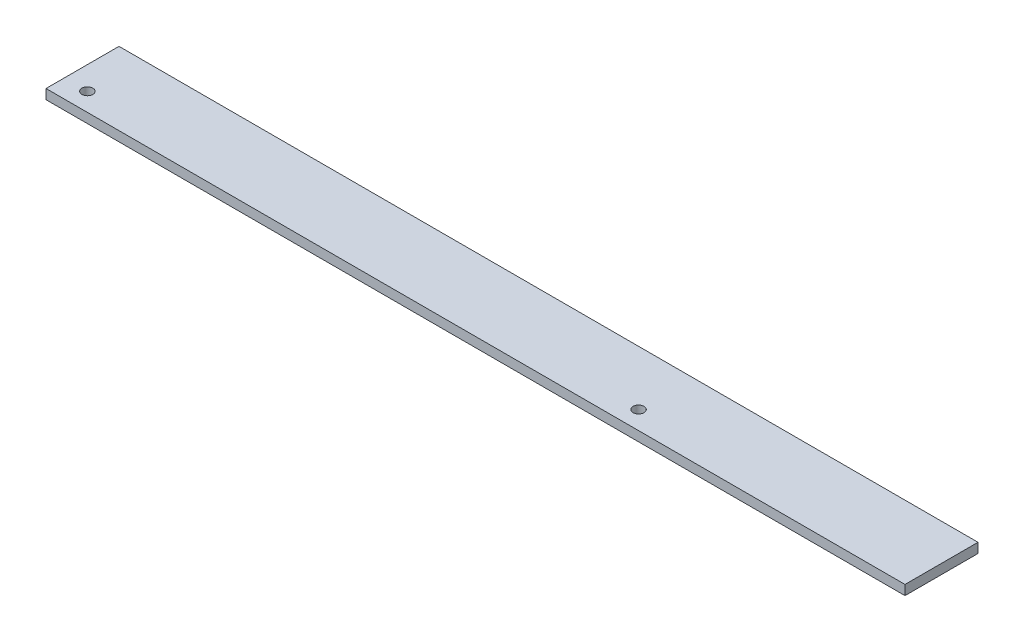
SolidWorks part; units mm, degrees
ref_plane "Спереди" through (0, 0, 0) normal (0, 0, 1) x (1, 0, 0)
ref_plane "Сверху" through (0, 0, 0) normal (0, 1, 0) x (1, 0, 0)
ref_plane "Справа" through (0, 0, 0) normal (1, 0, 0) x (0, 0, -1)
sketch "Эскиз1" plane through (0, 0, 0) normal (1, 0, 0) x (0, 0, -1)
  line L1 (-15, -2) -> (15, -2)
  line L2 (-15, -2) -> (-15, 2)
  line L3 (-15, 2) -> (15, 2)
  line L4 (15, -2) -> (15, 2)
  line L5 (-15, -2) -> (15, 2) construction
  line L6 (-15, 2) -> (15, -2) construction
  point P0 (0, 0)
  dimension "D1" = 4
  dimension "D2" = 30
extrude "Бобышка-Вытянуть1" add sketch "Эскиз1" along normal blind 353
sketch "Эскиз2" plane through (0, 2, 0) normal (0, 1, 0) x (1, 0, 0)
  line L0 (0, 15) -> (0, -15) construction
  line L2 (353, 15) -> (353, -15) construction
  line L3 (353, -15) -> (0, -15) construction
  circle A0 centre (9.5, -7.5) radius 2.25
  circle A1 centre (236, -7.5) radius 2.25
  dimension "D1" = 4.5
  dimension "D2" = 9.5
  dimension "D4" = 117
  dimension "D5" = 7.5
  dimension "D6" = 4.5
  dimension "D7" = 7.5
extrude "Вырез-Вытянуть1" cut sketch "Эскиз2" against normal through all
